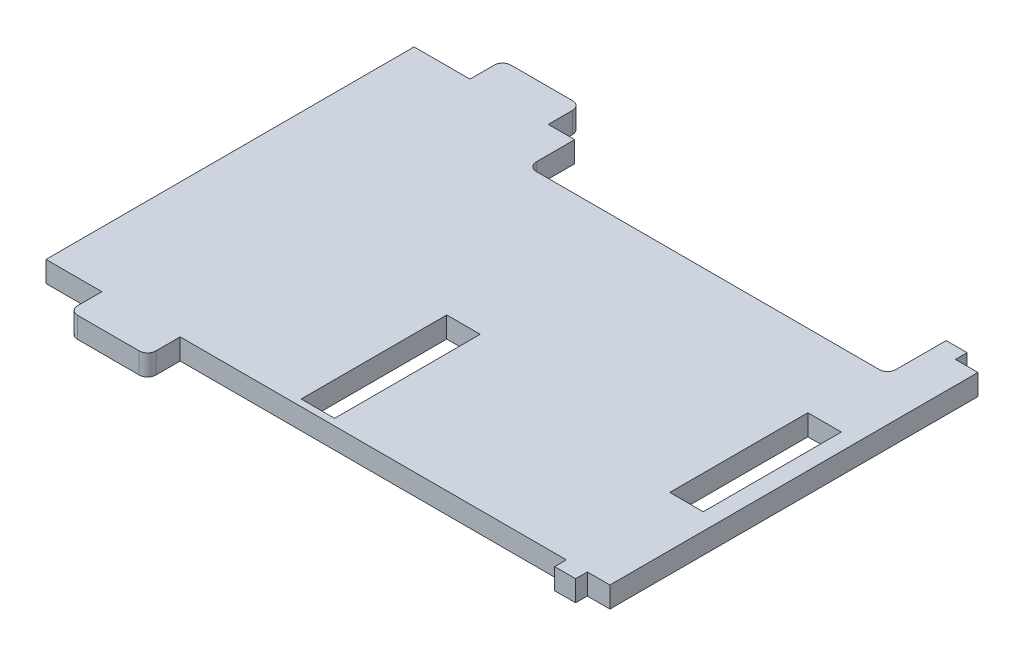
SolidWorks part; units mm, degrees
material "Custom Plastic"
ref_plane "Front Plane" through (0, 0, 0) normal (0, 0, 1) x (1, 0, 0)
ref_plane "Top Plane" through (0, 0, 0) normal (0, 1, 0) x (1, 0, 0)
ref_plane "Right Plane" through (0, 0, 0) normal (1, 0, 0) x (0, 0, -1)
sketch "Sketch1" plane through (0, 0, 0) normal (0, 1, 0) x (1, 0, 0)
  line L0 (36.195, 27.94) -> (36.195, 22.098)
  line L1 (-42.799, -27.94) -> (-34.3154, -27.94)
  line L2 (-42.799, -27.94) -> (-42.799, 27.94)
  line L3 (-42.799, 27.94) -> (-34.3154, 27.94)
  line L4 (42.799, -27.94) -> (42.799, 27.94)
  line L5 (-42.799, -27.94) -> (42.799, 27.94) construction
  line L6 (-42.799, 27.94) -> (42.799, -27.94) construction
  line L7 (34.925, 20.828) -> (-17.145, 20.828)
  line L8 (-18.415, 22.098) -> (-18.415, 27.94)
  line L9 (39.37, 27.94) -> (42.799, 27.94)
  line L10 (36.195, 27.94) -> (36.195, 29.718)
  line L11 (36.195, 29.718) -> (39.37, 29.718)
  line L12 (39.37, 29.718) -> (39.37, 27.94)
  line L13 (-42.799, 0) -> (42.799, 0) construction
  line L14 (35.179, 9.7282) -> (40.259, 9.7282)
  line L15 (35.179, 9.7282) -> (35.179, -11.2268)
  line L16 (35.179, -11.2268) -> (40.259, -11.2268)
  line L17 (40.259, 9.7282) -> (40.259, -11.2268)
  line L18 (39.37, -29.718) -> (39.37, -27.94)
  line L19 (36.195, -27.94) -> (36.195, -29.718)
  line L20 (36.195, -29.718) -> (39.37, -29.718)
  line L21 (39.37, -27.94) -> (42.799, -27.94)
  line L22 (-22.4282, 27.94) -> (-18.415, 27.94)
  line L23 (-22.4282, -27.94) -> (-22.4282, -31.623)
  line L24 (-34.3154, 27.94) -> (-34.3154, 31.623)
  line L25 (-33.0454, 32.893) -> (-23.6982, 32.893)
  line L26 (-22.4282, 27.94) -> (-22.4282, 31.623)
  line L27 (-33.0454, -32.893) -> (-23.6982, -32.893)
  line L28 (-34.3154, -27.94) -> (-34.3154, -31.623)
  line L29 (-22.4282, -27.94) -> (36.195, -27.94)
  line L31 (-5.08, -26.924) -> (0, -26.924)
  line L32 (-5.08, -26.924) -> (-5.08, -4.826)
  line L33 (-5.08, -4.826) -> (0, -4.826)
  line L34 (0, -26.924) -> (0, -4.826)
  arc A0 (34.925, 20.828) -> (36.195, 22.098) centre (34.925, 22.098) ccw
  arc A1 (-17.145, 20.828) -> (-18.415, 22.098) centre (-17.145, 22.098) cw
  arc A2 (-23.6982, 32.893) -> (-22.4282, 31.623) centre (-23.6982, 31.623) cw
  arc A3 (-33.0454, 32.893) -> (-34.3154, 31.623) centre (-33.0454, 31.623) ccw
  arc A4 (-23.6982, -32.893) -> (-22.4282, -31.623) centre (-23.6982, -31.623) ccw
  arc A5 (-33.0454, -32.893) -> (-34.3154, -31.623) centre (-33.0454, -31.623) cw
  point P0 (0, 0)
  point P29 (36.195, 20.828)
  point P32 (-18.415, 20.828)
  point P35 (-22.4282, 32.893)
  point P38 (-34.3154, 32.893)
  dimension "D15" = 1.27
  dimension "D16" = 1.27
  dimension "D17" = 1.27
  dimension "D18" = 1.27
  dimension "D1" = 85.598
  dimension "D2" = 55.88
  dimension "D3" = 54.61
  dimension "D4" = 6.604
  dimension "D5" = 7.112
  dimension "D6" = 1.778
  dimension "D7" = 3.175
  dimension "D8" = 20.955
  dimension "D9" = 5.08
  dimension "D10" = 2.54
  dimension "D11" = 16.7132
  dimension "D12" = 11.8872
  dimension "D13" = 4.953
  dimension "D14" = 8.4836
  dimension "D19" = 5.08
  dimension "D20" = 22.098
  dimension "D21" = 1.016
  dimension "D22" = 17.3482
extrude "Boss-Extrude1" add sketch "Sketch1" along normal blind 3.175
